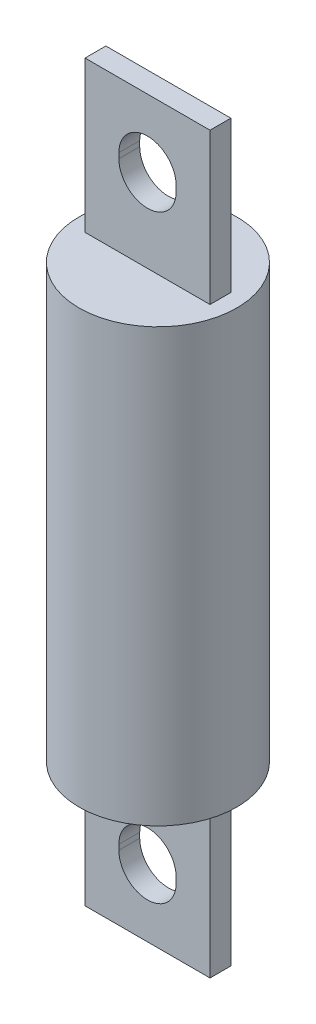
SolidWorks part; units mm, degrees
ref_plane "X-Y Datum" through (0, 0, 0) normal (0, 0, 1) x (1, 0, 0)
ref_plane "X-Z Datum" through (0, 0, 0) normal (0, 1, 0) x (1, 0, 0)
ref_plane "Y-Z Datum" through (0, 0, 0) normal (1, 0, 0) x (0, 0, -1)
sketch "Sketch1" plane through (0, 0, 0) normal (0, 1, 0) x (1, 0, 0)
  circle A0 centre (0, 0) radius 12.0269
extrude "Boss-Extrude1" add sketch "Sketch1" along normal blind 65.8876
sketch "Sketch2" plane through (0, 65.8876, 0) normal (0, 1, 0) x (1, 0, 0)
  line L1 (-9.525, -1.5875) -> (9.525, -1.5875)
  line L2 (-9.525, -1.5875) -> (-9.525, 1.5875)
  line L3 (-9.525, 1.5875) -> (9.525, 1.5875)
  line L4 (9.525, -1.5875) -> (9.525, 1.5875)
  line L5 (-9.525, -1.5875) -> (9.525, 1.5875) construction
  line L6 (-9.525, 1.5875) -> (9.525, -1.5875) construction
  point P0 (0, 0)
extrude "Boss-Extrude2" add sketch "Sketch2" along normal blind 23.0124
ref_plane "Plane1" through (0, 32.9438, 0) normal (0, 1, 0) x (1, 0, 0)
sketch "Sketch3" plane through (0, 0, 1.5875) normal (0, 0, 1) x (1, 0, 0)
  line L0 (0, 32.9438) -> (0, 78.1939) construction
  line L1 (13.2296, 32.9438) -> (-13.2296, 32.9438) construction
  line L2 (0, 32.9438) -> (0, 78.9851) construction
  line L3 (-4.3688, 78.9851) -> (-4.3688, 78.1939)
  line L4 (4.3688, 78.9851) -> (4.3688, 78.1939)
  arc A0 (4.3688, 78.9851) -> (-4.3688, 78.9851) centre (0, 78.9851) ccw
  arc A1 (-4.3688, 78.1939) -> (4.3688, 78.1939) centre (0, 78.1939) ccw
extrude "Cut-Extrude1" cut sketch "Sketch3" against normal through all
mirror "Mirror2" about plane through (0, 32.9438, 0) normal (0, 1, 0) of "Cut-Extrude1", "Boss-Extrude2"
